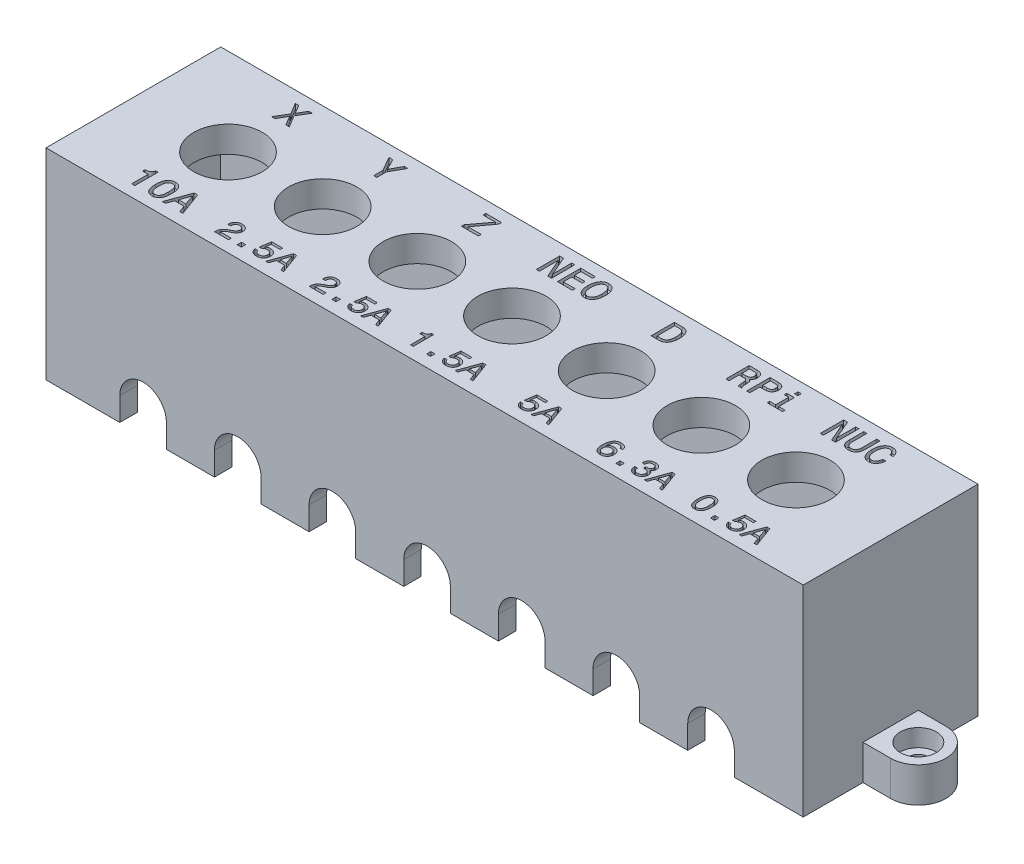
SolidWorks part; units mm, degrees
ref_plane "Front Plane" through (0, 0, 0) normal (0, 0, 1) x (1, 0, 0)
ref_plane "Top Plane" through (0, 0, 0) normal (0, 1, 0) x (1, 0, 0)
ref_plane "Right Plane" through (0, 0, 0) normal (1, 0, 0) x (0, 0, -1)
sketch "Sketch1" plane through (0, 0, 0) normal (0, 1, 0) x (1, 0, 0)
  line L1 (-130, 15) -> (0, 15)
  line L2 (-130, 15) -> (-130, -15)
  line L3 (-130, -15) -> (0, -15)
  line L4 (0, 15) -> (0, -15)
  point P4 (0, 0)
  dimension "D1" = 130
  dimension "D2" = 30
extrude "Boss-Extrude1" add sketch "Sketch1" along normal blind 4.5
sketch "Sketch2" plane through (0, 4.5, 0) normal (0, 1, 0) x (1, 0, 0)
  line L0 (-130, 0) -> (0, 0) construction
  line L1 (-130, 15) -> (-130, -15) construction
  circle A0 centre (-113.75, 0) radius 5.875
  circle A1 centre (-97.5, 0) radius 5.875
  circle A2 centre (-81.25, 0) radius 5.875
  circle A3 centre (-48.75, 0) radius 5.875
  circle A4 centre (-65, 0) radius 5.875
  circle A5 centre (-32.5, 0) radius 5.875
  circle A6 centre (-16.25, 0) radius 5.875
  dimension "D7" = 11.75
  dimension "D1" = 130
  dimension "D2" = 16.25
  dimension "D3" = 32.5
  dimension "D4" = 48.75
  dimension "D5" = 81.25
  dimension "D6" = 65
  dimension "D8" = 97.5
  dimension "D9" = 113.75
extrude "Cut-Extrude1" cut sketch "Sketch2" against normal through all
sketch "Sketch3" plane through (0, 4.5, 0) normal (0, 1, 0) x (1, 0, 0)
  line L0 (-119.625, 0) -> (-119.625, 15) construction
  line L1 (0, 15) -> (-130, 15) construction
  line L2 (-107.875, 0) -> (-107.875, 15) construction
  line L3 (-107.875, 9) -> (-119.625, 9) construction
  line L4 (-103.375, 0) -> (-103.375, 15) construction
  line L5 (-91.625, 0) -> (-91.625, 15) construction
  line L6 (-103.375, 9) -> (-91.625, 9) construction
  line L7 (-87.125, 0) -> (-87.125, 15) construction
  line L8 (-75.375, 0) -> (-75.375, 15) construction
  line L9 (-87.125, 9) -> (-75.375, 9) construction
  line L10 (-54.625, 0) -> (-54.625, 15) construction
  line L11 (-42.875, 0) -> (-42.875, 15) construction
  line L12 (-54.625, 9) -> (-42.875, 9) construction
  line L13 (-70.875, 0) -> (-70.875, 15) construction
  line L14 (-59.125, 0) -> (-59.125, 15) construction
  line L15 (-70.875, 9) -> (-59.125, 9) construction
  line L16 (-119.625, 0) -> (-119.625, -15) construction
  line L17 (-130, -15) -> (0, -15) construction
  line L18 (-107.875, 0) -> (-107.875, -15) construction
  line L19 (-103.375, 0) -> (-103.375, -15) construction
  line L20 (-91.625, 0) -> (-91.625, -15) construction
  line L21 (-87.125, 0) -> (-87.125, -15) construction
  line L22 (-75.375, 0) -> (-75.375, -15) construction
  line L23 (-54.625, 0) -> (-54.625, -15) construction
  line L24 (-42.875, 0) -> (-42.875, -15) construction
  line L25 (-70.875, 0) -> (-70.875, -15) construction
  line L26 (-59.125, 0) -> (-59.125, -15) construction
  line L27 (-119.625, -13) -> (-107.875, -13) construction
  line L28 (-103.375, -13) -> (-91.625, -13) construction
  line L29 (-87.125, -13) -> (-75.375, -13) construction
  line L30 (-54.625, -13) -> (-42.875, -13) construction
  line L31 (-70.875, -13) -> (-59.125, -13) construction
  line L32 (-38.375, 15) -> (-38.375, 0) construction
  line L33 (-38.375, 0) -> (-38.375, -15) construction
  line L34 (-26.625, -15) -> (-26.625, 0) construction
  line L35 (-26.625, 0) -> (-26.625, 15) construction
  line L36 (-22.125, 0) -> (-22.125, 15) construction
  line L37 (-22.125, 0) -> (-22.125, -15) construction
  line L38 (-10.375, 0) -> (-10.375, 15) construction
  line L39 (-10.375, 0) -> (-10.375, -15) construction
  line L40 (-38.375, -13) -> (-26.625, -13) construction
  line L41 (-22.125, -13) -> (-10.375, -13) construction
  line L42 (-38.375, 9) -> (-26.625, 9) construction
  line L43 (-22.125, 9) -> (-10.375, 9) construction
  circle A0 centre (-113.75, 0) radius 5.875 construction
  circle A1 centre (-97.5, 0) radius 5.875 construction
  circle A2 centre (-81.25, 0) radius 5.875 construction
  circle A3 centre (-48.75, 0) radius 5.875 construction
  circle A4 centre (-65, 0) radius 5.875 construction
  circle A8 centre (-32.5, 0) radius 5.875 construction
  circle A9 centre (-16.25, 0) radius 5.875 construction
  text T0 "X" font "Monospac821 BT" height 4
  text T1 "Y" font "Monospac821 BT" height 4
  text T2 "Z" font "Monospac821 BT" height 4
  text T3 "D" font "Monospac821 BT" height 4
  text T4 "NEO" font "Monospac821 BT" height 4
  text T5 "10A" font "Monospac821 BT" height 4
  text T6 "2.5A" font "Monospac821 BT" height 3.5
  text T7 "2.5A" font "Monospac821 BT" height 3.5
  text T8 "5A" font "Monospac821 BT" height 3.5
  text T9 "1.5A" font "Monospac821 BT" height 3.5
  text T10 "RPi" font "Monospac821 BT" height 4
  text T11 "NUC" font "Monospac821 BT" height 4
  text T12 "6.3A" font "Monospac821 BT" height 3.5
  text T13 "0.5A" font "Monospac821 BT" height 3.5
  dimension "D1" = 2
  dimension "D2" = 6
extrude "Cut-Extrude2" cut sketch "Sketch3" against normal blind 1
sketch "Sketch4" plane through (0, 0, 0) normal (0, -1, 0) x (1, 0, 0)
  line L0 (-130, 15) -> (-130, -15)
  line L1 (-130, -15) -> (0, -15)
  line L2 (0, -15) -> (0, 15)
  line L3 (-127, 12) -> (-127, -12)
  line L4 (-127, -12) -> (-3, -12)
  line L5 (-3, -12) -> (-3, 12)
  line L9 (-127, 15) -> (-127, -12) construction
  line L10 (-130, 12) -> (0, 12)
  line L11 (-127, 12) -> (-3, 12)
  line L12 (-3, -12) -> (-3, 15) construction
  line L15 (-130, 15) -> (0, 15)
  dimension "D1" = 3
  dimension "D2" = 3
extrude "Boss-Extrude2" add sketch "Sketch4" along normal blind 30
sketch "Sketch5" plane through (0, -30, 0) normal (0, -1, 0) x (1, 0, 0)
  line L4 (-134.75, 4.75) -> (-130, 4.75)
  line L5 (-130, 15) -> (-130, -15) construction
  line L6 (-130, 4.75) -> (-130, -4.75)
  line L7 (-130, -4.75) -> (-134.75, -4.75)
  line L8 (4.75, 4.75) -> (0, 4.75)
  line L9 (0, -15) -> (0, 15) construction
  line L10 (0, 4.75) -> (0, -4.75)
  line L11 (0, -4.75) -> (4.75, -4.75)
  arc A1 (4.75, -4.75) -> (4.75, 4.75) centre (4.75, 0) ccw
  arc A2 (-134.75, 4.75) -> (-134.75, -4.75) centre (-134.75, 0) ccw
  point P10 (-130, 0)
  point P11 (0, 0)
  point P22 (0, 0)
  dimension "D1" = 4.75
  dimension "D2" = 4.75
extrude "Boss-Extrude3" add sketch "Sketch5" against normal blind 6
sketch "Sketch6" plane through (0, -24, 0) normal (0, 1, 0) x (1, 0, 0)
  point P0 (4.75, 0)
  point P6 (-134.75, 0)
hole_wizard "CBORE for M3 SHCS1" positions "Sketch6" profile "Sketch7" counterbore size "M3" standard "ANSI Metric" end condition through all
sketch "Sketch7" plane through (4.75, -24, 0) normal (1, 0, 0) x (0, 0, 1)
  line L0 (0, 0) -> (0, 6)
  line L1 (0, 6) -> (1.7, 6)
  line L3 (1.7, 6) -> (1.7, 3)
  line L4 (1.7, 3) -> (3.1, 3)
  line L5 (3.1, 3) -> (3.1, 0)
  line L7 (3.1, 0) -> (0, 0)
  line L11 (0, -6.35) -> (0, 107.95) construction
  dimension "Thru Hole Dia." = 3.4
  dimension "Thru Hole Depth" = 6
  dimension "C'Bore Dia." = 6.2
  dimension "C'Bore Depth" = 3
sketch "Sketch8" plane through (0, 0, 15) normal (0, 0, 1) x (1, 0, 0)
  line L0 (-117.3333, -26) -> (-117.3333, -30)
  line L1 (0, -30) -> (-130, -30) construction
  line L2 (-109.3333, -26) -> (-109.3333, -30)
  line L3 (-109.3333, -30) -> (-117.3333, -30)
  line L5 (-130, 4.5) -> (-130, -30) construction
  arc A0 (-109.3333, -26) -> (-117.3333, -26) centre (-113.3333, -26) ccw
  dimension "D1" = 4
  dimension "D2" = 4
  dimension "D3" = 16.6667
extrude "Cut-Extrude3" cut sketch "Sketch8" against normal up to surface (3 mm away) up to face at (-65, -15, 12)
pattern_linear "LPattern1" count 7 spacing 16.25 along (1, 0, 0) of "Cut-Extrude3"
equation "\"D2@Sketch2\"=\"D1@Sketch2\"/8"
equation "\"D3@Sketch2\"=\"D1@Sketch2\"/8*2"
equation "\"D4@Sketch2\"=\"D1@Sketch2\"/8*3"
equation "\"D5@Sketch2\"=\"D1@Sketch2\"/8*5"
equation "\"D6@Sketch2\"=\"D1@Sketch2\"/8*4"
equation "\"D2@Sketch8\"=\"D1@Sketch8\""
equation "\"D3@Sketch8\"=100/6"
equation "\"D3@LPattern1\"=16.25"
equation "\"D8@Sketch2\"=\"D1@Sketch2\"/8*6"
equation "\"D9@Sketch2\"=\"D1@Sketch2\"/8*7"
equation "\"D2@Sketch5\"=9.5-\"D1@Sketch5\""
